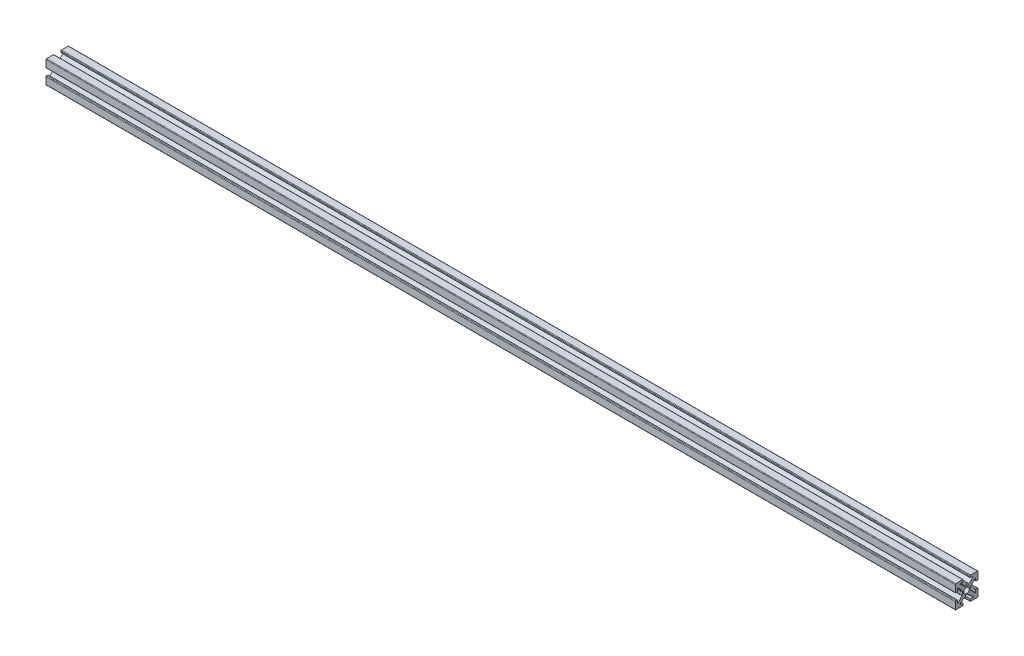
SolidWorks part; units mm, degrees
material "Acciaio in lega fuso"
ref_plane "Front Plane" through (0, 0, 0) normal (0, 0, 1) x (1, 0, 0)
ref_plane "Top Plane" through (0, 0, 0) normal (0, 1, 0) x (1, 0, 0)
ref_plane "Right Plane" through (0, 0, 0) normal (1, 0, 0) x (0, 0, -1)
sketch "Sketch1" plane through (0, 0, 0) normal (1, 0, 0) x (0, 0, -1)
  line L0 (0, 0) -> (0, 1.4986) construction
  line L1 (-0.2413, 1.4986) -> (0.2413, 1.4986)
  line L2 (5.0038, 1.7526) -> (5.0038, 4.7498)
  line L3 (0.7493, 2.0066) -> (0.8899, 2.0066)
  line L4 (1.0639, 2.0756) -> (2.8908, 3.7937)
  line L5 (2.8038, 4.0132) -> (1.7526, 4.0132)
  line L6 (1.4986, 4.2672) -> (1.4986, 4.7498)
  line L7 (1.7526, 5.0038) -> (4.7498, 5.0038)
  line L8 (5.0038, 5.0038) -> (0, 0) construction
  line L9 (0, 0) -> (8.6271, 0) construction
  line L10 (0, 0) -> (0, 5.0038) construction
  line L11 (4.2672, 1.4986) -> (4.7498, 1.4986)
  line L12 (4.0132, 2.8038) -> (4.0132, 1.7526)
  line L13 (2.0756, 1.0639) -> (3.7937, 2.8908)
  line L14 (2.0066, 0.7493) -> (2.0066, 0.8899)
  line L15 (1.4986, -0.2413) -> (1.4986, 0.2413)
  line L16 (0, 0) -> (1.4986, 0) construction
  line L17 (-0.2413, -1.4986) -> (0.2413, -1.4986)
  line L18 (0.7493, -2.0066) -> (0.8899, -2.0066)
  line L19 (1.0639, -2.0756) -> (2.8908, -3.7937)
  line L20 (2.8038, -4.0132) -> (1.7526, -4.0132)
  line L21 (1.4986, -4.2672) -> (1.4986, -4.7498)
  line L22 (1.7526, -5.0038) -> (4.7498, -5.0038)
  line L23 (5.0038, -1.7526) -> (5.0038, -4.7498)
  line L24 (4.2672, -1.4986) -> (4.7498, -1.4986)
  line L25 (4.0132, -2.8038) -> (4.0132, -1.7526)
  line L26 (2.0756, -1.0639) -> (3.7937, -2.8908)
  line L27 (2.0066, -0.7493) -> (2.0066, -0.8899)
  line L28 (-0.7493, 2.0066) -> (-0.8899, 2.0066)
  line L29 (-1.0639, 2.0756) -> (-2.8908, 3.7937)
  line L30 (-2.8038, 4.0132) -> (-1.7526, 4.0132)
  line L31 (-1.4986, 4.2672) -> (-1.4986, 4.7498)
  line L32 (-1.7526, 5.0038) -> (-4.7498, 5.0038)
  line L33 (-5.0038, 1.7526) -> (-5.0038, 4.7498)
  line L34 (-4.2672, 1.4986) -> (-4.7498, 1.4986)
  line L35 (-4.0132, 2.8038) -> (-4.0132, 1.7526)
  line L36 (-2.0756, 1.0639) -> (-3.7937, 2.8908)
  line L37 (-2.0066, 0.7493) -> (-2.0066, 0.8899)
  line L38 (-1.4986, -0.2413) -> (-1.4986, 0.2413)
  line L39 (-2.0066, -0.7493) -> (-2.0066, -0.8899)
  line L40 (-2.0756, -1.0639) -> (-3.7937, -2.8908)
  line L41 (-4.0132, -2.8038) -> (-4.0132, -1.7526)
  line L42 (-4.2672, -1.4986) -> (-4.7498, -1.4986)
  line L43 (-5.0038, -1.7526) -> (-5.0038, -4.7498)
  line L44 (-1.7526, -5.0038) -> (-4.7498, -5.0038)
  line L45 (-1.4986, -4.2672) -> (-1.4986, -4.7498)
  line L46 (-2.8038, -4.0132) -> (-1.7526, -4.0132)
  line L47 (-1.0639, -2.0756) -> (-2.8908, -3.7937)
  line L48 (-0.7493, -2.0066) -> (-0.8899, -2.0066)
  arc A0 (2.8908, 3.7937) -> (2.8038, 4.0132) centre (2.8038, 3.8862) ccw
  arc A1 (0.4953, 1.7526) -> (0.7493, 2.0066) centre (0.7493, 1.7526) cw
  arc A2 (0.8899, 2.0066) -> (1.0639, 2.0756) centre (0.8899, 2.2606) ccw
  arc A3 (1.7526, 4.0132) -> (1.4986, 4.2672) centre (1.7526, 4.2672) cw
  arc A4 (1.4986, 4.7498) -> (1.7526, 5.0038) centre (1.7526, 4.7498) cw
  arc A5 (0.2413, 1.4986) -> (0.4953, 1.7526) centre (0.2413, 1.7526) ccw
  arc A6 (4.7498, 1.4986) -> (5.0038, 1.7526) centre (4.7498, 1.7526) ccw
  arc A7 (4.0132, 1.7526) -> (4.2672, 1.4986) centre (4.2672, 1.7526) ccw
  arc A8 (3.7937, 2.8908) -> (4.0132, 2.8038) centre (3.8862, 2.8038) cw
  arc A9 (2.0066, 0.8899) -> (2.0756, 1.0639) centre (2.2606, 0.8899) cw
  arc A10 (1.7526, 0.4953) -> (2.0066, 0.7493) centre (1.7526, 0.7493) ccw
  arc A11 (1.4986, 0.2413) -> (1.7526, 0.4953) centre (1.7526, 0.2413) cw
  arc A12 (0.2413, -1.4986) -> (0.4953, -1.7526) centre (0.2413, -1.7526) cw
  arc A13 (0.4953, -1.7526) -> (0.7493, -2.0066) centre (0.7493, -1.7526) ccw
  arc A14 (0.8899, -2.0066) -> (1.0639, -2.0756) centre (0.8899, -2.2606) cw
  arc A15 (2.8908, -3.7937) -> (2.8038, -4.0132) centre (2.8038, -3.8862) cw
  arc A16 (1.7526, -4.0132) -> (1.4986, -4.2672) centre (1.7526, -4.2672) ccw
  arc A17 (1.4986, -4.7498) -> (1.7526, -5.0038) centre (1.7526, -4.7498) ccw
  arc A18 (4.7498, -1.4986) -> (5.0038, -1.7526) centre (4.7498, -1.7526) cw
  arc A19 (4.0132, -1.7526) -> (4.2672, -1.4986) centre (4.2672, -1.7526) cw
  arc A20 (3.7937, -2.8908) -> (4.0132, -2.8038) centre (3.8862, -2.8038) ccw
  arc A21 (2.0066, -0.8899) -> (2.0756, -1.0639) centre (2.2606, -0.8899) ccw
  arc A22 (1.7526, -0.4953) -> (2.0066, -0.7493) centre (1.7526, -0.7493) cw
  arc A23 (1.4986, -0.2413) -> (1.7526, -0.4953) centre (1.7526, -0.2413) ccw
  arc A24 (-0.2413, 1.4986) -> (-0.4953, 1.7526) centre (-0.2413, 1.7526) cw
  arc A25 (-0.4953, 1.7526) -> (-0.7493, 2.0066) centre (-0.7493, 1.7526) ccw
  arc A26 (-0.8899, 2.0066) -> (-1.0639, 2.0756) centre (-0.8899, 2.2606) cw
  arc A27 (-2.8908, 3.7937) -> (-2.8038, 4.0132) centre (-2.8038, 3.8862) cw
  arc A28 (-1.7526, 4.0132) -> (-1.4986, 4.2672) centre (-1.7526, 4.2672) ccw
  arc A29 (-1.4986, 4.7498) -> (-1.7526, 5.0038) centre (-1.7526, 4.7498) ccw
  arc A30 (-4.7498, 1.4986) -> (-5.0038, 1.7526) centre (-4.7498, 1.7526) cw
  arc A31 (-4.0132, 1.7526) -> (-4.2672, 1.4986) centre (-4.2672, 1.7526) cw
  arc A32 (-3.7937, 2.8908) -> (-4.0132, 2.8038) centre (-3.8862, 2.8038) ccw
  arc A33 (-2.0066, 0.8899) -> (-2.0756, 1.0639) centre (-2.2606, 0.8899) ccw
  arc A34 (-1.7526, 0.4953) -> (-2.0066, 0.7493) centre (-1.7526, 0.7493) cw
  arc A35 (-1.4986, 0.2413) -> (-1.7526, 0.4953) centre (-1.7526, 0.2413) ccw
  arc A36 (-1.4986, -0.2413) -> (-1.7526, -0.4953) centre (-1.7526, -0.2413) cw
  arc A37 (-1.7526, -0.4953) -> (-2.0066, -0.7493) centre (-1.7526, -0.7493) ccw
  arc A38 (-2.0066, -0.8899) -> (-2.0756, -1.0639) centre (-2.2606, -0.8899) cw
  arc A39 (-3.7937, -2.8908) -> (-4.0132, -2.8038) centre (-3.8862, -2.8038) cw
  arc A40 (-4.0132, -1.7526) -> (-4.2672, -1.4986) centre (-4.2672, -1.7526) ccw
  arc A41 (-4.7498, -1.4986) -> (-5.0038, -1.7526) centre (-4.7498, -1.7526) ccw
  arc A42 (-1.4986, -4.7498) -> (-1.7526, -5.0038) centre (-1.7526, -4.7498) cw
  arc A43 (-1.7526, -4.0132) -> (-1.4986, -4.2672) centre (-1.7526, -4.2672) cw
  arc A44 (-2.8908, -3.7937) -> (-2.8038, -4.0132) centre (-2.8038, -3.8862) ccw
  arc A45 (-0.8899, -2.0066) -> (-1.0639, -2.0756) centre (-0.8899, -2.2606) ccw
  arc A46 (-0.4953, -1.7526) -> (-0.7493, -2.0066) centre (-0.7493, -1.7526) cw
  arc A47 (-0.2413, -1.4986) -> (-0.4953, -1.7526) centre (-0.2413, -1.7526) ccw
  arc A48 (-4.7498, 5.0038) -> (-5.0038, 4.7498) centre (-4.7498, 4.7498) ccw
  arc A49 (-5.0038, -4.7498) -> (-4.7498, -5.0038) centre (-4.7498, -4.7498) ccw
  arc A50 (4.7498, -5.0038) -> (5.0038, -4.7498) centre (4.7498, -4.7498) ccw
  arc A51 (4.7498, 5.0038) -> (5.0038, 4.7498) centre (4.7498, 4.7498) cw
  point P14 (3.1242, 4.0132)
  point P19 (0.9906, 2.0066)
  point P150 (0, -1.4986)
  point P152 (-5.0038, 5.0038)
  point P155 (-5.0038, -5.0038)
  point P158 (5.0038, -5.0038)
  dimension "D10" = 0.127
  dimension "D11" = 0.254
  dimension "D2" = 0.254
  dimension "D1" = 10.0076
  dimension "D3" = 2.9972
  dimension "D4" = 0.508
  dimension "D5" = 2.9972
  dimension "D6" = 0.9906
  dimension "D7" = 1.6256
  dimension "D8" = 1.9812
  dimension "D9" = 0.9906
extrude "Estrusione-Estrusione1" add sketch "Sketch1" along normal blind 400 contours L36 A32 L35 A31 L34 A30 L33 A48 L32 A29 L31 A28 L30 A27 L29 A26 L28 A25 A24 L1 A5 A1 L3 A2 L4 A0 L5 A3 L6 A4 L7 A51 L2 A6 L11 A7 L12 A8 L13 A9 L14 A10 A11 L15 A23 A22 L27 A21 L26 A20 L25 A19 L24 A18 L23 A50 L22 A17 L21 A16 L20 A15 L19 A14 L18 A13 A12 L17 A47 A46 L48 A45 L47 A44 L46 A43 L45 A42 L44 A49 L43 A41 L42 A40 L41 A39 L40 A38 L39 A37 A36 L38 A35 A34 L37 A33
hole_wizard "Foro filettato M3x0.5-1" positions "Schizzo2" profile "Schizzo1" tap size "M3x0.5" standard "Ansi Metric" end condition through all
sketch "Schizzo2" plane through (0, 0, 0) normal (-1, 0, 0) x (0, 0, 1)
  point P0 (0, 0)
sketch "Schizzo1" plane through (0, 0, 0) normal (0, 1, 0) x (0, 0, 1)
  line L0 (0, 0) -> (0, 400)
  line L1 (0, 400) -> (1.25, 400)
  line L2 (1.25, 400) -> (1.25, 0)
  line L5 (1.25, 0) -> (0, 0)
  line L11 (0, -6.35) -> (0, 107.95) construction
  dimension "Thread Major Dia." = 2.5
  dimension "Thru Tap Drill Depth" = 400
